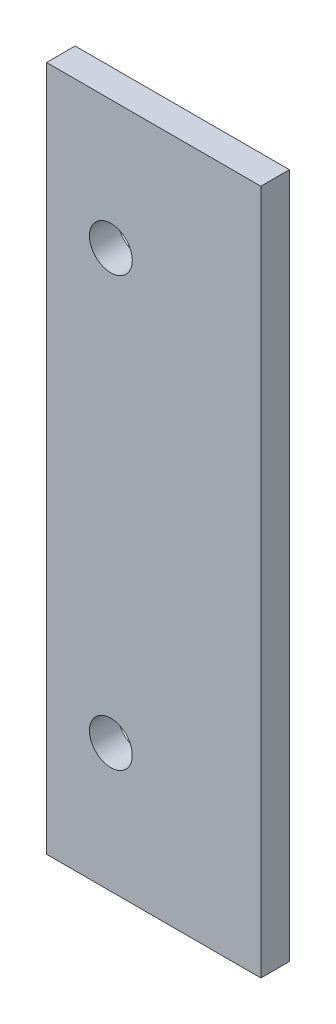
SolidWorks part; units mm, degrees
ref_plane "Plan de face" through (0, 0, 0) normal (0, 0, 1) x (1, 0, 0)
ref_plane "Plan de dessus" through (0, 0, 0) normal (0, 1, 0) x (1, 0, 0)
ref_plane "Plan de droite" through (0, 0, 0) normal (1, 0, 0) x (0, 0, -1)
sketch "Esquisse1" plane through (0, 0, 0) normal (0, 0, 1) x (1, 0, 0)
  line L0 (0, 0) -> (15, 0)
  line L1 (15, 0) -> (15, -48)
  line L2 (15, -48) -> (0, -48)
  line L3 (0, -48) -> (0, 0)
  line L4 (9, 0) -> (9, -48) construction
  line L5 (9, -24) -> (0, -24) construction
  line L6 (4.5, -24) -> (4.5, -9) construction
  circle A0 centre (4.5, -9) radius 1.5
  circle A1 centre (4.5, -39) radius 1.5
extrude "Extrusion1" add sketch "Esquisse1" along normal blind 2
